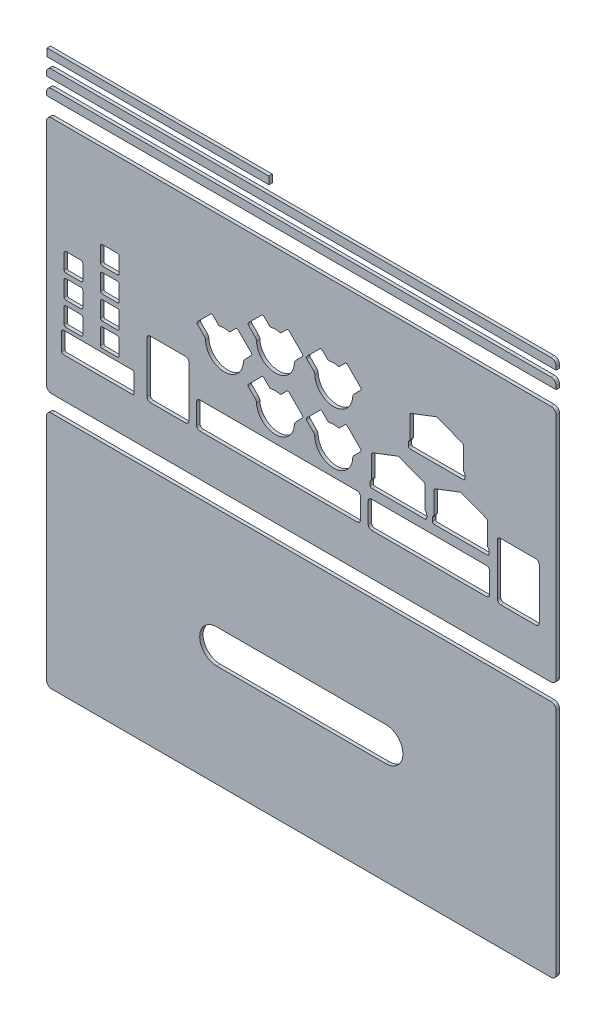
SolidWorks part; units mm, degrees
other "协会版图-顶面"
other "协会版图-长边"
other "协会版图-长边2"
other "协会版图-短边"
other "协会版图-底面"
ref_plane "前视基准面" through (0, 0, 0) normal (0, 0, 1) x (1, 0, 0)
ref_plane "上视基准面" through (0, 0, 0) normal (0, 1, 0) x (1, 0, 0)
ref_plane "右视基准面" through (0, 0, 0) normal (1, 0, 0) x (0, 0, -1)
sketch "草图1" plane through (0, 0, 0) normal (0, 0, 1) x (1, 0, 0)
  line L0 (-5, 136) -> (296, 136)
  line L1 (0, 0) -> (291, 0) construction
  line L2 (0, 0) -> (0, 131) construction
  line L3 (0, 131) -> (291, 131) construction
  line L4 (291, 0) -> (291, 131) construction
  line L5 (296, -5) -> (296, 136)
  line L6 (-5, -5) -> (296, -5)
  line L7 (-5, -5) -> (-5, 136)
  line L8 (146.1106, 88.7345) -> (137.617, 97.2281) construction
  line L9 (137.617, 97.2281) -> (133.4289, 93.0401) construction
  line L10 (126.9441, 93.0401) -> (122.7677, 97.2164) construction
  line L11 (122.7677, 97.2164) -> (114.3461, 88.7948) construction
  line L12 (114.3461, 88.7948) -> (118.5428, 84.5981) construction
  line L13 (146.1106, 88.7345) -> (141.9742, 84.5981) construction
  line L14 (180.5484, 88.7345) -> (172.0548, 97.2281) construction
  line L15 (172.0548, 97.2281) -> (167.8667, 93.0401) construction
  line L16 (161.3819, 93.0401) -> (157.2055, 97.2164) construction
  line L17 (157.2055, 97.2164) -> (148.7839, 88.7948) construction
  line L18 (148.7839, 88.7948) -> (152.9806, 84.5981) construction
  line L19 (180.5484, 88.7345) -> (176.412, 84.5981) construction
  line L20 (180.5022, 57.2605) -> (172.0085, 65.7542) construction
  line L21 (172.0085, 65.7542) -> (167.8205, 61.5662) construction
  line L22 (161.3356, 61.5662) -> (157.1593, 65.7425) construction
  line L23 (157.1593, 65.7425) -> (148.7377, 57.3208) construction
  line L24 (148.7377, 57.3208) -> (152.9344, 53.1241) construction
  line L25 (180.5022, 57.2605) -> (176.3658, 53.1241) construction
  line L26 (146.1106, 57.2605) -> (137.617, 65.7542) construction
  line L27 (137.617, 65.7542) -> (133.4289, 61.5662) construction
  line L28 (126.9441, 61.5662) -> (122.7677, 65.7425) construction
  line L29 (122.7677, 65.7425) -> (114.3461, 57.3208) construction
  line L30 (114.3461, 57.3208) -> (118.5428, 53.1241) construction
  line L31 (146.1106, 57.2605) -> (141.9742, 53.1241) construction
  line L32 (115.973, 74.1947) -> (107.4793, 82.6884) construction
  line L33 (107.4793, 82.6884) -> (103.2913, 78.5004) construction
  line L34 (96.8064, 78.5004) -> (92.6301, 82.6767) construction
  line L35 (92.6301, 82.6767) -> (84.2085, 74.255) construction
  line L36 (84.2085, 74.255) -> (88.4052, 70.0584) construction
  line L37 (115.973, 74.1947) -> (111.8366, 70.0584) construction
  line L38 (107.4793, 83.3955) -> (103.1526, 79.0688)
  line L39 (116.6801, 74.1947) -> (107.4793, 83.3955)
  line L40 (116.6801, 74.1947) -> (112.1901, 69.7048)
  line L41 (83.5014, 74.255) -> (88.0516, 69.7048)
  line L42 (92.6301, 83.3838) -> (83.5014, 74.255)
  line L43 (96.9451, 79.0688) -> (92.6301, 83.3838)
  line L44 (137.617, 97.9352) -> (133.2902, 93.6085)
  line L45 (146.8177, 88.7345) -> (137.617, 97.9352)
  line L46 (146.8177, 88.7345) -> (142.3277, 84.2446)
  line L47 (113.639, 88.7948) -> (118.1893, 84.2446)
  line L48 (122.7677, 97.9236) -> (113.639, 88.7948)
  line L49 (127.0828, 93.6085) -> (122.7677, 97.9236)
  line L50 (172.0548, 97.9352) -> (167.728, 93.6085)
  line L51 (181.2555, 88.7345) -> (172.0548, 97.9352)
  line L52 (181.2555, 88.7345) -> (176.7655, 84.2446)
  line L53 (148.0768, 88.7948) -> (152.6271, 84.2446)
  line L54 (157.2055, 97.9236) -> (148.0768, 88.7948)
  line L55 (161.5206, 93.6085) -> (157.2055, 97.9236)
  line L56 (172.0085, 66.4613) -> (167.6818, 62.1346)
  line L57 (181.2093, 57.2605) -> (172.0085, 66.4613)
  line L58 (181.2093, 57.2605) -> (176.7193, 52.7706)
  line L59 (148.0306, 57.3208) -> (152.5808, 52.7706)
  line L60 (157.1593, 66.4496) -> (148.0306, 57.3208)
  line L61 (161.4743, 62.1346) -> (157.1593, 66.4496)
  line L62 (137.617, 66.4613) -> (133.2902, 62.1346)
  line L63 (146.8177, 57.2605) -> (137.617, 66.4613)
  line L64 (146.8177, 57.2605) -> (142.3277, 52.7706)
  line L65 (113.639, 57.3208) -> (118.1893, 52.7706)
  line L66 (122.7677, 66.4496) -> (113.639, 57.3208)
  line L67 (127.0828, 62.1346) -> (122.7677, 66.4496)
  line L68 (210.1498, 90.4605) -> (225.4449, 96.3518) construction
  line L69 (240.74, 90.4605) -> (225.4449, 96.3518) construction
  line L70 (240.74, 76.8781) -> (240.74, 90.4605) construction
  line L71 (241.6993, 75.6663) -> (240.74, 76.8781) construction
  line L72 (241.6993, 73.1325) -> (241.6993, 75.6663) construction
  line L73 (209.1905, 73.1325) -> (241.6993, 73.1325) construction
  line L74 (209.1905, 73.1325) -> (209.1905, 75.6663) construction
  line L75 (209.1905, 75.6663) -> (210.1498, 76.8781) construction
  line L76 (210.1498, 76.8781) -> (210.1498, 90.4605) construction
  line L77 (241.24, 90.8037) -> (225.4449, 96.8876)
  line L78 (209.6498, 90.8037) -> (225.4449, 96.8876)
  line L79 (209.6498, 77.0521) -> (209.6498, 90.8037)
  line L80 (208.6905, 75.8403) -> (209.6498, 77.0521)
  line L81 (208.6905, 72.6325) -> (208.6905, 75.8403)
  line L82 (208.6905, 72.6325) -> (242.1993, 72.6325)
  line L83 (242.1993, 72.6325) -> (242.1993, 75.8403)
  line L84 (242.1993, 75.8403) -> (241.24, 77.0521)
  line L85 (241.24, 77.0521) -> (241.24, 90.8037)
  line L86 (218.6251, 59.3392) -> (202.83, 65.4231)
  line L87 (187.0349, 59.3392) -> (202.83, 65.4231)
  line L88 (187.0349, 45.5876) -> (187.0349, 59.3392)
  line L89 (186.0756, 44.3758) -> (187.0349, 45.5876)
  line L90 (186.0756, 41.168) -> (186.0756, 44.3758)
  line L91 (186.0756, 41.168) -> (219.5844, 41.168)
  line L92 (219.5844, 41.168) -> (219.5844, 44.3758)
  line L93 (219.5844, 44.3758) -> (218.6251, 45.5876)
  line L94 (218.6251, 45.5876) -> (218.6251, 59.3392)
  line L95 (255.4508, 59.3392) -> (239.6557, 65.4231)
  line L96 (223.8606, 59.3392) -> (239.6557, 65.4231)
  line L97 (223.8606, 45.5876) -> (223.8606, 59.3392)
  line L98 (222.9013, 44.3758) -> (223.8606, 45.5876)
  line L99 (222.9013, 41.168) -> (222.9013, 44.3758)
  line L100 (222.9013, 41.168) -> (256.4101, 41.168)
  line L101 (256.4101, 41.168) -> (256.4101, 44.3758)
  line L102 (256.4101, 44.3758) -> (255.4508, 45.5876)
  line L103 (255.4508, 45.5876) -> (255.4508, 59.3392)
  line L104 (26.937, 60.9701) -> (37.937, 60.9701)
  line L105 (56.3034, 53.6282) -> (77.1351, 53.6282)
  line L106 (54.3034, 51.6282) -> (54.3034, 21.6438)
  line L107 (56.3034, 19.6438) -> (77.1351, 19.6438)
  line L108 (79.1351, 51.6282) -> (79.1351, 21.6438)
  line L109 (85.6411, 35.567) -> (178.4632, 35.567)
  line L110 (83.6411, 33.567) -> (83.6411, 21.6438)
  line L111 (85.6411, 19.6438) -> (178.4632, 19.6438)
  line L112 (180.4632, 33.567) -> (180.4632, 21.6438)
  line L113 (186.9926, 35.567) -> (254.7717, 35.567)
  line L114 (184.9926, 33.567) -> (184.9926, 21.6438)
  line L115 (186.9926, 19.6438) -> (254.7717, 19.6438)
  line L116 (256.7717, 33.567) -> (256.7717, 21.6438)
  line L117 (284.0232, 53.5853) -> (263.2536, 53.5853)
  line L118 (286.0232, 51.5853) -> (286.0232, 21.6438)
  line L119 (284.0232, 19.6438) -> (263.2536, 19.6438)
  line L120 (261.2536, 51.5853) -> (261.2536, 21.6438)
  line L121 (37.937, 71.9701) -> (37.937, 60.9701)
  line L122 (26.937, 71.9701) -> (37.937, 71.9701)
  line L123 (26.937, 71.9701) -> (26.937, 60.9701)
  line L124 (16.437, 71.9701) -> (16.437, 60.9701)
  line L125 (5.437, 60.9701) -> (16.437, 60.9701)
  line L126 (5.437, 71.9701) -> (5.437, 60.9701)
  line L127 (5.437, 71.9701) -> (16.437, 71.9701)
  line L128 (16.437, 58.0701) -> (16.437, 47.0701)
  line L129 (5.437, 47.0701) -> (16.437, 47.0701)
  line L130 (5.437, 58.0701) -> (5.437, 47.0701)
  line L131 (5.437, 58.0701) -> (16.437, 58.0701)
  line L132 (16.437, 44.1701) -> (16.437, 33.1701)
  line L133 (5.437, 33.1701) -> (16.437, 33.1701)
  line L134 (5.437, 44.1701) -> (5.437, 33.1701)
  line L135 (5.437, 44.1701) -> (16.437, 44.1701)
  line L136 (37.937, 58.0701) -> (37.937, 47.0701)
  line L137 (26.937, 47.0701) -> (37.937, 47.0701)
  line L138 (26.937, 58.0701) -> (26.937, 47.0701)
  line L139 (26.937, 58.0701) -> (37.937, 58.0701)
  line L140 (37.937, 44.1701) -> (37.937, 33.1701)
  line L141 (26.937, 33.1701) -> (37.937, 33.1701)
  line L142 (26.937, 44.1701) -> (26.937, 33.1701)
  line L143 (26.937, 44.1701) -> (37.937, 44.1701)
  line L144 (26.937, 75.277) -> (37.937, 75.277)
  line L145 (37.937, 86.277) -> (37.937, 75.277)
  line L146 (26.937, 86.277) -> (37.937, 86.277)
  line L147 (26.937, 86.277) -> (26.937, 75.277)
  line L149 (3.9555, 30.9874) -> (46.8376, 30.9874)
  line L150 (3.9555, 30.9874) -> (3.9555, 18.524)
  line L151 (3.9555, 18.524) -> (46.8376, 18.524)
  line L152 (46.8376, 30.9874) -> (46.8376, 18.524)
  arc A0 (126.9441, 93.0401) -> (133.4289, 93.0401) centre (130.1865, 83.2994) cw construction
  arc A1 (118.5428, 84.5981) -> (119.5465, 82.1745) centre (116.1197, 82.175) cw construction
  arc A2 (119.5465, 82.1745) -> (140.9083, 82.1745) centre (130.2274, 82.9011) ccw construction
  arc A3 (141.9742, 84.5981) -> (140.9083, 82.1745) centre (144.5556, 82.0167) ccw construction
  arc A4 (161.3819, 93.0401) -> (167.8667, 93.0401) centre (164.6243, 83.2994) cw construction
  arc A5 (152.9806, 84.5981) -> (153.9843, 82.1745) centre (150.5575, 82.175) cw construction
  arc A6 (153.9843, 82.1745) -> (175.3461, 82.1745) centre (164.6652, 82.9011) ccw construction
  arc A7 (176.412, 84.5981) -> (175.3461, 82.1745) centre (178.9934, 82.0167) ccw construction
  arc A8 (161.3356, 61.5662) -> (167.8205, 61.5662) centre (164.5781, 51.8254) cw construction
  arc A9 (152.9344, 53.1241) -> (153.9381, 50.7005) centre (150.5113, 50.701) cw construction
  arc A10 (153.9381, 50.7005) -> (175.2999, 50.7005) centre (164.619, 51.4271) ccw construction
  arc A11 (176.3658, 53.1241) -> (175.2999, 50.7005) centre (178.9472, 50.5427) ccw construction
  arc A12 (126.9441, 61.5662) -> (133.4289, 61.5662) centre (130.1865, 51.8254) cw construction
  arc A13 (118.5428, 53.1241) -> (119.5465, 50.7005) centre (116.1197, 50.701) cw construction
  arc A14 (119.5465, 50.7005) -> (140.9083, 50.7005) centre (130.2274, 51.4271) ccw construction
  arc A15 (141.9742, 53.1241) -> (140.9083, 50.7005) centre (144.5556, 50.5427) ccw construction
  arc A16 (96.8064, 78.5004) -> (103.2913, 78.5004) centre (100.0489, 68.7596) cw construction
  arc A17 (88.4052, 70.0584) -> (89.4089, 67.6348) centre (85.9821, 67.6352) cw construction
  arc A18 (89.4089, 67.6348) -> (110.7707, 67.6348) centre (100.0898, 68.3613) ccw construction
  arc A19 (111.8366, 70.0584) -> (110.7707, 67.6348) centre (114.418, 67.4769) ccw construction
  arc A20 (96.9451, 79.0688) -> (103.1526, 79.0688) centre (100.0489, 68.7596) cw
  arc A21 (112.1901, 69.7048) -> (111.27, 67.6073) centre (114.418, 67.4769) ccw
  arc A22 (88.9088, 67.6187) -> (111.27, 67.6073) centre (100.0898, 68.3613) ccw
  arc A23 (88.0516, 69.7048) -> (88.9088, 67.6187) centre (85.9821, 67.6352) cw
  arc A24 (127.0828, 93.6085) -> (133.2902, 93.6085) centre (130.1865, 83.2994) cw
  arc A25 (142.3277, 84.2446) -> (141.4076, 82.147) centre (144.5556, 82.0167) ccw
  arc A26 (119.0465, 82.1584) -> (141.4076, 82.147) centre (130.2274, 82.9011) ccw
  arc A27 (118.1893, 84.2446) -> (119.0465, 82.1584) centre (116.1197, 82.175) cw
  arc A28 (161.5206, 93.6085) -> (167.728, 93.6085) centre (164.6243, 83.2994) cw
  arc A29 (176.7655, 84.2446) -> (175.8454, 82.147) centre (178.9934, 82.0167) ccw
  arc A30 (153.4843, 82.1584) -> (175.8454, 82.147) centre (164.6652, 82.9011) ccw
  arc A31 (152.6271, 84.2446) -> (153.4843, 82.1584) centre (150.5575, 82.175) cw
  arc A32 (161.4743, 62.1346) -> (167.6818, 62.1346) centre (164.5781, 51.8254) cw
  arc A33 (176.7193, 52.7706) -> (175.7992, 50.6731) centre (178.9472, 50.5427) ccw
  arc A34 (153.438, 50.6845) -> (175.7992, 50.6731) centre (164.619, 51.4271) ccw
  arc A35 (152.5808, 52.7706) -> (153.438, 50.6845) centre (150.5113, 50.701) cw
  arc A36 (127.0828, 62.1346) -> (133.2902, 62.1346) centre (130.1865, 51.8254) cw
  arc A37 (142.3277, 52.7706) -> (141.4076, 50.6731) centre (144.5556, 50.5427) ccw
  arc A38 (119.0465, 50.6845) -> (141.4076, 50.6731) centre (130.2274, 51.4271) ccw
  arc A39 (118.1893, 52.7706) -> (119.0465, 50.6845) centre (116.1197, 50.701) cw
  arc A40 (286.0232, 21.6438) -> (284.0232, 19.6438) centre (284.0232, 21.6438) cw
  arc A41 (284.0232, 53.5853) -> (286.0232, 51.5853) centre (284.0232, 51.5853) cw
  arc A42 (263.2536, 53.5853) -> (261.2536, 51.5853) centre (263.2536, 51.5853) ccw
  arc A43 (263.2536, 19.6438) -> (261.2536, 21.6438) centre (263.2536, 21.6438) cw
  arc A44 (254.7717, 19.6438) -> (256.7717, 21.6438) centre (254.7717, 21.6438) ccw
  arc A45 (254.7717, 35.567) -> (256.7717, 33.567) centre (254.7717, 33.567) cw
  arc A46 (186.9926, 35.567) -> (184.9926, 33.567) centre (186.9926, 33.567) ccw
  arc A47 (184.9926, 21.6438) -> (186.9926, 19.6438) centre (186.9926, 21.6438) ccw
  arc A48 (178.4632, 19.6438) -> (180.4632, 21.6438) centre (178.4632, 21.6438) ccw
  arc A49 (178.4632, 35.567) -> (180.4632, 33.567) centre (178.4632, 33.567) cw
  arc A50 (83.6411, 21.6438) -> (85.6411, 19.6438) centre (85.6411, 21.6438) ccw
  arc A51 (85.6411, 35.567) -> (83.6411, 33.567) centre (85.6411, 33.567) ccw
  arc A52 (77.1351, 19.6438) -> (79.1351, 21.6438) centre (77.1351, 21.6438) ccw
  arc A53 (54.3034, 21.6438) -> (56.3034, 19.6438) centre (56.3034, 21.6438) ccw
  arc A54 (77.1351, 53.6282) -> (79.1351, 51.6282) centre (77.1351, 51.6282) cw
  arc A55 (56.3034, 53.6282) -> (54.3034, 51.6282) centre (56.3034, 51.6282) ccw
  dimension "D10" = 2
  dimension "D1" = 131
  dimension "D2" = 291
  dimension "D3" = 5
  dimension "D4" = 0.5
  dimension "D5" = 0.5
  dimension "D6" = 0.5
  dimension "D7" = 0.5
  dimension "D8" = 0.5
  dimension "D9" = 0.5
  dimension "D11" = 2
  dimension "D12" = 3
extrude "凸台-拉伸1" add sketch "草图1" against normal blind 2
fillet "圆角1" radius 3 4 edges at (296, 136, -1) (296, -5, -1) (-5, -5, -1) (-5, 136, -1)
fillet "圆角2" radius 1 99 edges at (103.1526, 79.0688, -1) (107.4793, 83.3955, -1) (116.6801, 74.1947, -1) (111.27, 67.6073, -1) (88.9088, 67.6187, -1) (83.5014, 74.255, -1) (92.6301, 83.3838, -1) (96.9451, 79.0688, -1) (133.2902, 93.6085, -1) (137.617, 97.9352, -1) (146.8177, 88.7345, -1) (141.4076, 82.147, -1) (119.0465, 82.1584, -1) (113.639, 88.7948, -1) (122.7677, 97.9236, -1) (127.0828, 93.6085, -1) (167.728, 93.6085, -1) (172.0548, 97.9352, -1) (181.2555, 88.7345, -1) (175.8454, 82.147, -1) (153.4843, 82.1584, -1) (148.0768, 88.7948, -1) (157.2055, 97.9236, -1) (161.5206, 93.6085, -1) (167.6818, 62.1346, -1) (172.0085, 66.4613, -1) (181.2093, 57.2605, -1) (175.7992, 50.6731, -1) (153.438, 50.6845, -1) (148.0306, 57.3208, -1) (157.1593, 66.4496, -1) (161.4743, 62.1346, -1) (133.2902, 62.1346, -1) (137.617, 66.4613, -1) (146.8177, 57.2605, -1) (141.4076, 50.6731, -1) (119.0465, 50.6845, -1) (113.639, 57.3208, -1) (122.7677, 66.4496, -1) (127.0828, 62.1346, -1) (241.24, 77.0521, -1) (242.1993, 75.8403, -1) (242.1993, 72.6325, -1) (208.6905, 72.6325, -1) (208.6905, 75.8403, -1) (209.6498, 77.0521, -1) (209.6498, 90.8037, -1) (225.4449, 96.8876, -1) (241.24, 90.8037, -1) (218.6251, 45.5876, -1) (219.5844, 44.3758, -1) (219.5844, 41.168, -1) (186.0756, 41.168, -1) (186.0756, 44.3758, -1) (187.0349, 45.5876, -1) (187.0349, 59.3392, -1) (202.83, 65.4231, -1) (218.6251, 59.3392, -1) (255.4508, 45.5876, -1) (256.4101, 44.3758, -1) (256.4101, 41.168, -1) (222.9013, 41.168, -1) (222.9013, 44.3758, -1) (223.8606, 45.5876, -1) (223.8606, 59.3392, -1) (239.6557, 65.4231, -1) (255.4508, 59.3392, -1) (26.937, 71.9701, -1) (37.937, 71.9701, -1) (37.937, 60.9701, -1) (26.937, 60.9701, -1) (26.937, 86.277, -1) (37.937, 86.277, -1) (37.937, 75.277, -1) (26.937, 75.277, -1) (16.437, 71.9701, -1) (16.437, 60.9701, -1) (5.437, 60.9701, -1) (16.437, 58.0701, -1) (16.437, 47.0701, -1) (5.437, 47.0701, -1) (5.437, 58.0701, -1) (16.437, 44.1701, -1) (16.437, 33.1701, -1) (5.437, 33.1701, -1) (5.437, 44.1701, -1) (37.937, 58.0701, -1) (37.937, 47.0701, -1) (26.937, 47.0701, -1) (26.937, 58.0701, -1) (37.937, 44.1701, -1) (37.937, 33.1701, -1) (26.937, 33.1701, -1) (26.937, 44.1701, -1) (3.9555, 30.9874, -1) (46.8376, 30.9874, -1) (46.8376, 18.524, -1) (3.9555, 18.524, -1) (5.437, 71.9701, -1)
sketch "草图2" plane through (0, 0, 0) normal (0, 0, 1) x (1, 0, 0)
  line L0 (293, 136) -> (-2, 136) construction
  line L1 (-5, 146) -> (296, 146)
  line L2 (-5, 146) -> (-5, 151)
  line L3 (-5, 151) -> (296, 151)
  line L4 (296, 146) -> (296, 151)
  line L5 (-5, 133) -> (-5, -2) construction
  line L6 (296, -2) -> (296, 133) construction
  dimension "D1" = 10
  dimension "D2" = 5
extrude "凸台-拉伸2" add sketch "草图2" against normal blind 2 separate body
fillet "圆角3" radius 3 2 edges at (-5, 151, -1) (296, 151, -1)
pattern_linear "阵列(线性)1" count 2 spacing 10 along (0, 1, 0) of bodies 107
sketch "草图3" plane through (0, 0, 0) normal (0, 0, 1) x (1, 0, 0)
  line L0 (293, 161) -> (-2, 161) construction
  line L1 (-4.6377, 166) -> (126.3623, 166)
  line L2 (-4.6377, 166) -> (-4.6377, 170.5)
  line L3 (-4.6377, 170.5) -> (126.3623, 170.5)
  line L4 (126.3623, 166) -> (126.3623, 170.5)
  dimension "D1" = 131
  dimension "D2" = 4.5
  dimension "D3" = 5
extrude "凸台-拉伸3" add sketch "草图3" against normal blind 2 separate body
sketch "草图4" plane through (0, 0, 0) normal (0, 0, 1) x (1, 0, 0)
  line L0 (-5, 133) -> (-5, -2) construction
  line L1 (-5, -15) -> (296, -15)
  line L2 (-5, -15) -> (-5, -156)
  line L3 (-5, -156) -> (296, -156)
  line L4 (296, -15) -> (296, -156)
  line L5 (-2, -5) -> (293, -5) construction
  dimension "D1" = 141
  dimension "D2" = 301
  dimension "D3" = 10
extrude "凸台-拉伸4" add sketch "草图4" against normal blind 2 separate body
fillet "圆角4" radius 3 4 edges at (-5, -156, -1) (296, -156, -1) (296, -15, -1) (-5, -15, -1)
sketch "草图6" plane through (0, 0, 0) normal (0, 0, 1) x (1, 0, 0)
  line L0 (95.5, -85.5) -> (195.5, -85.5) construction
  line L1 (95.5, -75.5) -> (195.5, -75.5)
  line L2 (95.5, -95.5) -> (195.5, -95.5)
  line L6 (95.5, -85.5) -> (-5, -85.5) construction
  line L7 (-5, -18) -> (-5, -153) construction
  line L8 (195.5, -85.5) -> (296, -85.5) construction
  line L9 (296, -153) -> (296, -18) construction
  line L10 (195.5, -85.5) -> (195.5, -15) construction
  line L11 (293, -15) -> (-2, -15) construction
  line L12 (195.5, -85.5) -> (195.5, -156) construction
  line L13 (-2, -156) -> (293, -156) construction
  arc A0 (95.5, -75.5) -> (95.5, -95.5) centre (95.5, -85.5) ccw
  arc A1 (195.5, -95.5) -> (195.5, -75.5) centre (195.5, -85.5) ccw
  point P2 (145.5, -85.5)
  dimension "D1" = 10
  dimension "D2" = 100
extrude "切除-拉伸1" cut sketch "草图6" against normal blind 2
other "保存实体1"
